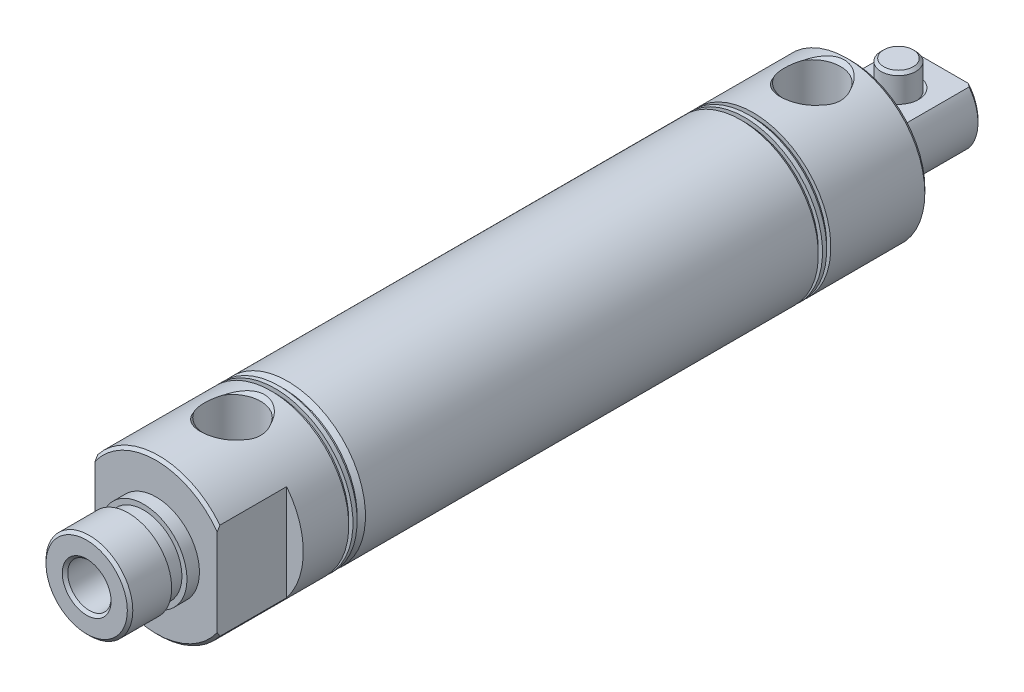
SolidWorks part; units mm, degrees
material "AISI 316 Annealed Stainless Steel Bar (SS)"
ref_plane "Front" through (0, 0, 0) normal (0, 0, 1) x (1, 0, 0)
ref_plane "Top" through (0, 0, 0) normal (0, 1, 0) x (1, 0, 0)
ref_plane "Right" through (0, 0, 0) normal (1, 0, 0) x (0, 0, -1)
sketch "Sketch1" plane through (0, 0, 0) normal (0, 0, 1) x (1, 0, 0)
  circle A0 centre (0, 0) radius 14.224
  dimension "E" = 28.448
extrude "Extrude1" add sketch "Sketch1" along normal up to surface (71.4375 mm away) and the other way up to surface (71.4375 mm away)
ref_plane "SwitchPlaneA" through (0, 0, 32.0615) normal (0, 0, 1) x (1, 0, 0)
ref_plane "SwitchPlaneB" through (0, 0, -22.6645) normal (0, 0, -1) x (-1, 0, 0)
sketch "Sketch2" plane through (0, 0, 0) normal (1, 0, 0) x (0, 0, -1)
  line L0 (0, 0) -> (-79.7053, 0) construction
  line L1 (-71.4375, 7.9248) -> (-73.7235, 7.9248)
  line L2 (-71.4375, 14.224) -> (-71.4375, -14.224) construction
  line L3 (-73.7235, 7.9248) -> (-73.7235, 7)
  line L4 (-76.5235, 7.9375) -> (-84.1375, 7.9375)
  line L5 (-84.1375, 7.9375) -> (-84.1375, 0)
  line L6 (-84.1375, 0) -> (-71.4375, 0)
  line L7 (-71.4375, 0) -> (-71.4375, 7.9248)
  line L8 (-76.5235, 7.9375) -> (-76.5235, 7)
  line L9 (-76.5235, 7) -> (-73.7235, 7)
  dimension "D1" = 2.286
  dimension "NN" = 15.875
  dimension "B" = 15.8496
  dimension "D2" = 14
  dimension "W-K" = 12.7
  dimension "D3" = 2.8
revolve "Nose" add sketch "Sketch2" angle 360 about L0
sketch "Sketch3" plane through (0, 0, 0) normal (1, 0, 0) x (0, 0, -1)
  line L0 (0, 0) -> (-66.9635, 0) construction
  line L1 (71.4375, 14.224) -> (-71.4375, 14.224) construction
  line L2 (-50.419, 14.224) -> (-49.657, 14.224)
  line L3 (-50.419, 14.224) -> (-50.419, 13.462)
  line L4 (-50.419, 13.462) -> (-49.657, 13.462)
  line L5 (-49.657, 14.224) -> (-49.657, 13.462)
  line L6 (-48.895, 14.224) -> (-48.895, 13.462)
  line L7 (-48.895, 13.462) -> (-48.133, 13.462)
  line L8 (-48.133, 13.462) -> (-47.371, 14.224)
  line L9 (-47.371, 14.224) -> (-48.895, 14.224)
  line L10 (37.7405, 14.224) -> (37.7405, 13.462)
  line L11 (37.7405, 13.462) -> (36.9785, 14.224)
  line L12 (36.9785, 14.224) -> (37.7405, 14.224)
  line L13 (36.2165, 14.224) -> (36.2165, 13.462)
  line L14 (36.2165, 13.462) -> (35.4545, 14.224)
  line L15 (35.4545, 14.224) -> (36.2165, 14.224)
  line L16 (-71.4375, 14.224) -> (-71.4375, -14.224) construction
  line L17 (71.4375, -14.224) -> (71.4375, 14.224) construction
  dimension "D1" = 0.762
  dimension "D2" = 33.697
  dimension "D3" = 21.0185
  dimension "D4" = 0.762
  dimension "D5" = 45
  dimension "D6" = 1.524
  dimension "D7" = 0.762
revolve "CoverGrooves" cut sketch "Sketch3" angle 360 about L0
sketch "Sketch7" plane through (0, 0, 0) normal (1, 0, 0) x (0, 0, -1)
  line L0 (-57.4675, 0) -> (-57.4675, 19.911) construction
  line L1 (-57.4675, 14.224) -> (-51.6175, 14.224)
  line L2 (-50.419, 14.224) -> (-71.4375, 14.224) construction
  line L3 (-51.6175, 14.224) -> (-52.3175, 13.524)
  line L4 (-52.3175, 13.524) -> (-52.3175, 0)
  line L5 (-52.3175, 0) -> (-57.4675, 0)
  line L6 (-57.4675, 0) -> (-57.4675, 14.224)
  line L7 (-84.1375, 7.9375) -> (-84.1375, -7.9375) construction
  line L8 (-47.371, 14.224) -> (-48.133, 13.462) construction
  dimension "D1" = 10.3
  dimension "D2" = 0.7
  dimension "Y-K" = 26.67
revolve "FrontPort" cut sketch "Sketch7" angle 360 about L0
sketch "Sketch8" plane through (0, 0, 84.1375) normal (0, 0, 1) x (1, 0, 0)
  circle A0 centre (0, 0) radius 3.9624
  dimension "MM" = 7.9248
extrude "RodHole" cut sketch "Sketch8" against normal up to surface (112.0375 mm away)
sketch "Sketch9" plane through (0, 0, -27.9) normal (0, 0, 1) x (1, 0, 0)
  circle A0 centre (0, 0) radius 13.4938
  dimension "Bore" = 26.9875
extrude "StrokeChamber" cut sketch "Sketch9" along normal up to surface (55.8 mm away)
chamfer "Chamfer1" distance 0.5 angle 45 4 edges at (14.224, 0, -71.4375) (14.224, 0, 71.4375) (-7.9375, 0, 84.1375) (3.9624, 0, 84.1375)
sketch "Sketch4" plane through (0, 0, 0) normal (0, 1, 0) x (1, 0, 0)
  line L0 (0, 0) -> (0, 54.4802) construction
  line L2 (14.224, -71.4375) -> (11.176, -71.4375)
  line L3 (14.224, -71.4375) -> (14.224, -58.7375)
  line L4 (14.224, -58.7375) -> (11.176, -58.7375)
  line L5 (11.176, -71.4375) -> (11.176, -58.7375)
  line L6 (14.224, 65.3415) -> (13.724, 65.3415)
  line L7 (14.224, 65.3415) -> (14.224, 71.4375)
  line L8 (14.224, 71.4375) -> (13.724, 71.4375)
  line L9 (13.724, 65.3415) -> (13.724, 71.4375)
  line L10 (-14.224, 0) -> (14.224, 0) construction
  line L11 (-14.224, -71.4375) -> (14.224, -71.4375) construction
  line L12 (14.224, 71.4375) -> (-14.224, 71.4375) construction
  line L13 (-13.724, 65.3415) -> (-13.724, 71.4375)
  line L14 (-14.224, 71.4375) -> (-13.724, 71.4375)
  line L15 (-14.224, 65.3415) -> (-14.224, 71.4375)
  line L16 (-14.224, 65.3415) -> (-13.724, 65.3415)
  line L17 (-11.176, -71.4375) -> (-11.176, -58.7375)
  line L18 (-14.224, -58.7375) -> (-11.176, -58.7375)
  line L19 (-14.224, -71.4375) -> (-14.224, -58.7375)
  line L20 (-14.224, -71.4375) -> (-11.176, -71.4375)
  line L21 (-14.224, 0) -> (14.224, 0) construction
  dimension "D1" = 12.7
  dimension "NC" = 27.448
  dimension "N" = 22.352
  dimension "NE" = 6.096
extrude "Flats" cut sketch "Sketch4" against normal through all and the other way through all
sketch "Sketch10" [suppressed] plane through (0, 0, 0) normal (1, 0, 0) x (0, 0, -1)
  line L0 (0, 0) -> (-22.9719, 0) construction
  line L1 (71.501, 0) -> (71.501, 5.85)
  line L2 (71.501, 5.85) -> (70.801, 5.15)
  line L3 (70.801, 5.15) -> (0, 5.15)
  line L4 (0, 5.15) -> (0, 0)
  line L5 (0, 0) -> (71.501, 0)
  line L6 (-47.4345, 14.224) -> (-48.1965, 13.462) construction
  line L8 (71.501, -14.224) -> (71.501, 14.224) construction
  dimension "D1" = 10.3
  dimension "D2" = 0.7
revolve "RearStdPort" [suppressed] cut sketch "Sketch10" angle 360 about L0
sketch "Sketch11" plane through (0, 0, 0) normal (1, 0, 0) x (0, 0, -1)
  line L0 (0, 0) -> (65.1253, 0) construction
  line L1 (71.4375, 7.4375) -> (70.9375, 7.9375)
  line L2 (70.9375, 7.9375) -> (58.9431, 7.9375)
  line L3 (58.9431, 7.9375) -> (58.9431, 7)
  line L4 (58.9431, 7) -> (57.9755, 7)
  line L5 (57.9755, 7) -> (57.9755, 7.9375)
  line L6 (57.9755, 7.9375) -> (55.6895, 7.9375)
  line L7 (55.6895, 7.9375) -> (55.6895, 13.462)
  line L8 (55.6895, 13.462) -> (54.9275, 14.224)
  line L9 (35.4545, 14.224) -> (-47.371, 14.224) construction
  line L10 (54.9275, 14.224) -> (71.4375, 14.224)
  line L11 (71.4375, 7.4375) -> (71.4375, 14.224)
  line L16 (37.7405, 13.462) -> (36.9785, 14.224) construction
  line L17 (71.4375, -14.224) -> (71.4375, 14.224) construction
  dimension "D1" = 0.9676
  dimension "D2" = 2.286
  dimension "D3" = 15.875
  dimension "ZB-LB+L" = 15.748
  dimension "D4" = 14
revolve "EndThreads" cut sketch "Sketch11" angle 360 about L0
sketch "Sketch13" plane through (0, 0, 0) normal (1, 0, 0) x (0, 0, -1)
  line L0 (48.5794, 0) -> (48.5794, 52.324) construction
  line L1 (48.5794, 0) -> (53.7294, 0)
  line L2 (53.7294, 0) -> (53.7294, 13.524)
  line L3 (53.7294, 13.524) -> (54.4294, 14.224)
  line L5 (54.4294, 14.224) -> (48.5794, 14.224)
  line L6 (48.5794, 14.224) -> (48.5794, 0)
  line L10 (71.4375, -7.4375) -> (71.4375, 7.4375) construction
  line L11 (-47.371, 14.224) -> (-48.895, 14.224) construction
  line L12 (-52.3175, 0) -> (-57.4675, 0) construction
  line L13 (-51.6175, 14.224) -> (-52.3175, 13.524) construction
  dimension "D1" = 22.8581
revolve "RearTopPort" cut sketch "Sketch13" angle 360 about L0
sketch "Sketch12" plane through (0, 0, 0) normal (1, 0, 0) x (0, -1, 0)
  line L0 (0, 0) -> (0, 62.5586) construction
  line L1 (7.4375, 71.4375) -> (-7.4375, 71.4375) construction
  line L2 (14.224, 71.4375) -> (4.826, 71.4375)
  line L3 (14.224, 71.4375) -> (14.224, 56.0625)
  line L4 (14.224, 56.0625) -> (4.826, 56.0625)
  line L5 (4.826, 71.4375) -> (4.826, 56.0625)
  line L6 (-14.224, 0) -> (14.224, 0) construction
  line L7 (-4.826, 71.4375) -> (-4.826, 56.0625)
  line L8 (-14.224, 56.0625) -> (-4.826, 56.0625)
  line L9 (-14.224, 71.4375) -> (-14.224, 56.0625)
  line L10 (-14.224, 71.4375) -> (-4.826, 71.4375)
  line L12 (-14.224, 0) -> (14.224, 0) construction
  dimension "D1" = 15.375
  dimension "F" = 9.652
extrude "EndFlats" cut sketch "Sketch12" against normal through all and the other way through all
sketch "Sketch15" plane through (0, 0, 0) normal (1, 0, 0) x (0, -1, 0)
  line L0 (0, 64.3255) -> (21.0846, 64.3255) construction
  line L1 (4.826, 68.0132) -> (4.326, 67.5132)
  line L2 (4.826, 70.9375) -> (4.826, 58.9431) construction
  line L3 (4.326, 67.5132) -> (-4.326, 67.5132)
  line L4 (-4.326, 67.5132) -> (-4.826, 68.0132)
  line L5 (-4.826, 58.9431) -> (-4.826, 70.9375) construction
  line L6 (-4.826, 68.0132) -> (-4.826, 64.3255)
  line L7 (-4.826, 64.3255) -> (4.826, 64.3255)
  line L8 (4.826, 64.3255) -> (4.826, 68.0132)
  line L9 (13.462, 55.6895) -> (-13.462, 55.6895) construction
  dimension "D1" = 0.5
  dimension "G" = 6.3754
  dimension "L" = 8.636
revolve "ClevisPinHole" cut sketch "Sketch15" angle 360 about L0
sketch "Sketch18" plane through (0, 0, 0) normal (1, 0, 0) x (0, 0, -1)
  line L0 (64.3255, 0) -> (64.3255, 25.8254) construction
  line L2 (64.3255, 0) -> (64.3255, -21.0846) construction
  line L3 (64.3255, 9.525) -> (67.0132, 9.525)
  line L4 (67.0132, 9.525) -> (67.5132, 9.025)
  line L5 (67.5132, 9.025) -> (67.5132, -9.025)
  line L6 (67.5132, -9.025) -> (67.0132, -9.525)
  line L7 (67.0132, -9.525) -> (64.3255, -9.525)
  line L8 (64.3255, -9.525) -> (64.3255, 9.525)
  line L9 (67.5132, -4.326) -> (67.5132, 4.326) construction
  point P13 (64.3255, 0)
  dimension "D1" = 0.5
  dimension "GB" = 19.05
revolve "ClevisPin" add sketch "Sketch18" angle 360 about L0
ref_plane "Plane1" through (0, 13.524, 0) normal (0, 1, 0) x (-1, 0, 0)
